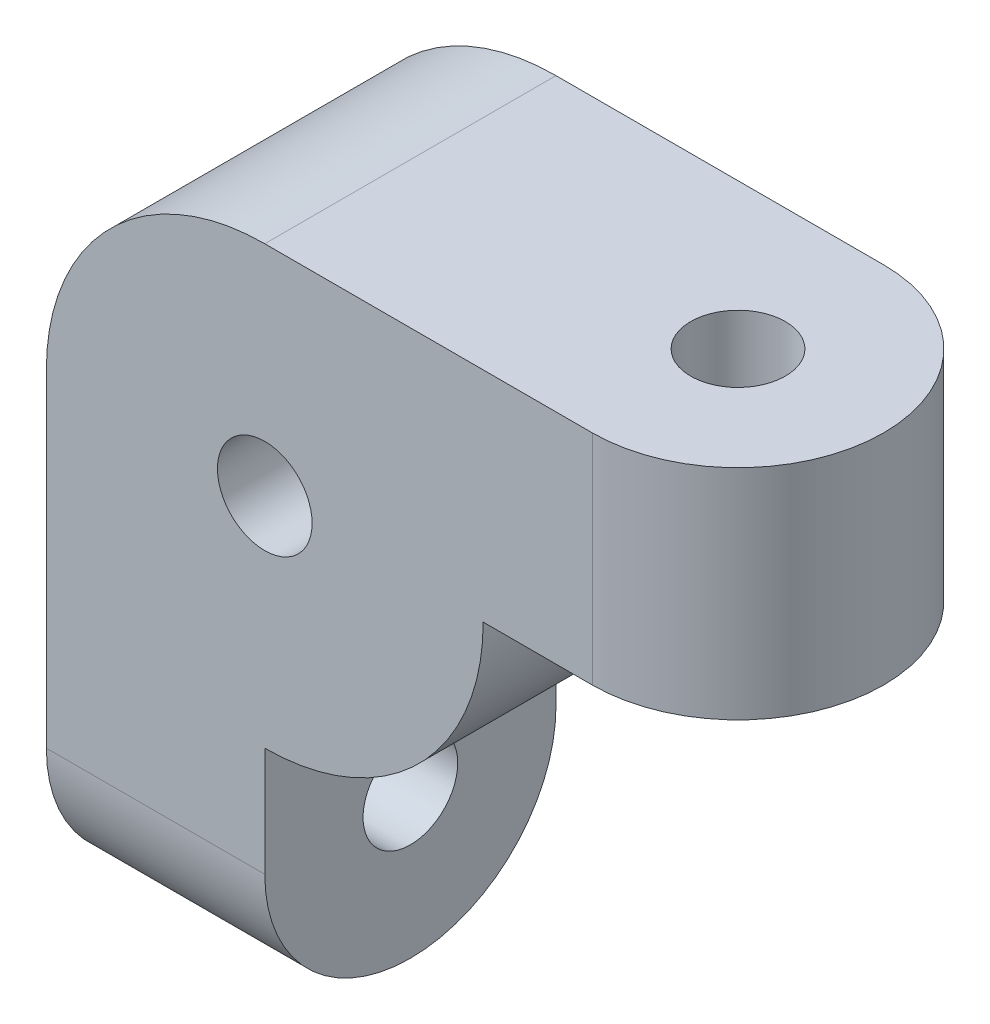
SolidWorks part; units mm, degrees
ref_plane "Front Plane" through (0, 0, 0) normal (0, 0, 1) x (1, 0, 0)
ref_plane "Top Plane" through (0, 0, 0) normal (0, 1, 0) x (1, 0, 0)
ref_plane "Right Plane" through (0, 0, 0) normal (1, 0, 0) x (0, 0, -1)
sketch "Sketch1" plane through (0, 0, 0) normal (0, 0, 1) x (1, 0, 0)
  line L0 (-6, 0) -> (-6, -6)
  line L1 (-6, -6) -> (0, -6)
  line L2 (0, 6) -> (6, 6)
  line L3 (6, 6) -> (6, 0)
  circle A0 centre (0, 0) radius 6
  circle A1 centre (0, 0) radius 1.3
  dimension "D1" = 12
  dimension "D2" = 2.6
extrude "Boss-Extrude1" add sketch "Sketch1" along normal blind 8 contours A0 A1 | A0 L0 L1 | A0 L3 L2
sketch "Sketch4" plane through (0, 0, 0) normal (1, 0, 0) x (0, 0, -1)
  line L1 (-8, -9) -> (0, -9)
  line L2 (-8, -9) -> (-8, -6)
  line L3 (-8, -6) -> (0, -6)
  line L4 (0, -6) -> (0, -9)
  arc A0 (-8, -9) -> (0, -9) centre (-4, -9) ccw
  dimension "D1" = 3
extrude "Boss-Extrude2" add sketch "Sketch4" against normal blind 6 contours L4 L3 L2 L1 | L1 A0
sketch "Sketch5" plane through (0, 0, 0) normal (0, 1, 0) x (1, 0, 0)
  line L1 (6, 0) -> (9, 0)
  line L2 (6, 0) -> (6, -8)
  line L3 (6, -8) -> (9, -8)
  arc A1 (9, -8) -> (9, 0) centre (9, -4) ccw
  dimension "D1" = 3
extrude "Boss-Extrude4" add sketch "Sketch5" along normal blind 6
sketch "Sketch12" plane through (0, 0, 0) normal (0, -1, 0) x (1, 0, 0)
  circle A0 centre (9, 4) radius 1.3
  dimension "D1" = 2.6
extrude "Cut-Extrude6" cut sketch "Sketch12" against normal blind 6
sketch "Sketch13" plane through (0, 0, 0) normal (1, 0, 0) x (0, 0, -1)
  circle A0 centre (-4, -9) radius 1.3
  dimension "D1" = 2.6
extrude "Cut-Extrude7" cut sketch "Sketch13" against normal blind 6
sketch "Sketch14" plane through (0, 0, 0) normal (0, 0, -1) x (-1, 0, 0)
  circle A0 centre (0, 0) radius 3
  dimension "D1" = 6
extrude "Cut-Extrude8" cut sketch "Sketch14" against normal blind 3
